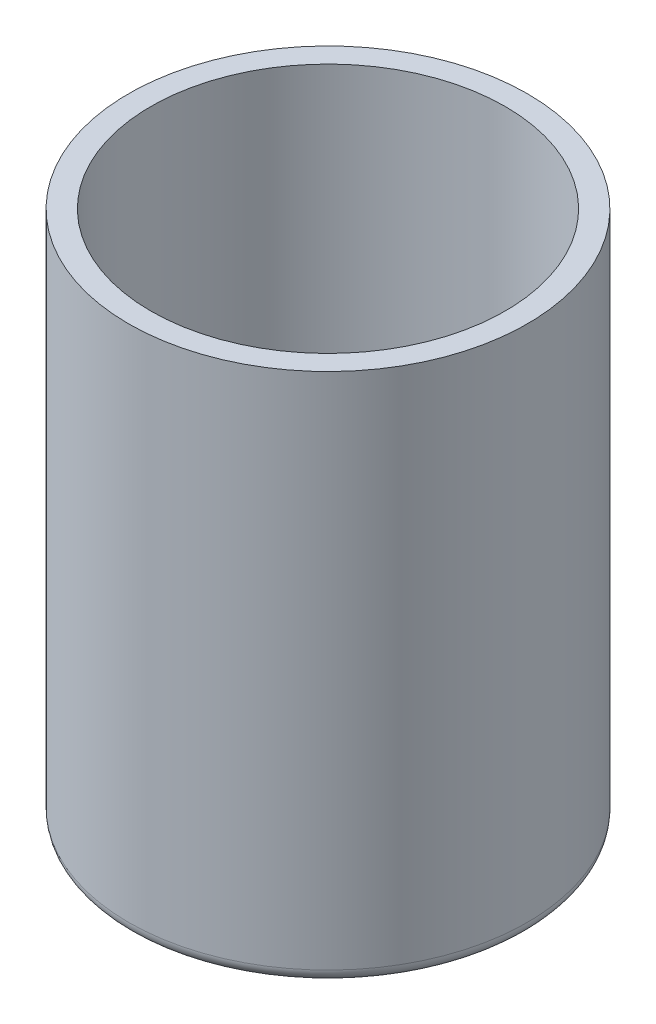
SolidWorks part; units mm, degrees
ref_plane "Front Plane" through (0, 0, 0) normal (0, 0, 1) x (1, 0, 0)
ref_plane "Top Plane" through (0, 0, 0) normal (0, 1, 0) x (1, 0, 0)
ref_plane "Right Plane" through (0, 0, 0) normal (1, 0, 0) x (0, 0, -1)
sketch "Sketch1" plane through (0, 0, 0) normal (0, 1, 0) x (1, 0, 0)
  circle A0 centre (0, 0) radius 45
extrude "Boss-Extrude1" add sketch "Sketch1" along normal blind 120
sketch "Sketch2" plane through (0, 0, 0) normal (0, 1, 0) x (1, 0, 0)
  circle A1 centre (30, 0) radius 6.2
  circle A2 centre (-30, 0) radius 6.2
sketch "Sketch3" plane through (0, 120, 0) normal (0, 1, 0) x (1, 0, 0)
  circle A0 centre (0, 0) radius 40
extrude "Cut-Extrude1" cut sketch "Sketch3" against normal blind 115
extrude "Cut-Extrude2" cut sketch "Sketch2" along normal up to surface (5 mm away) up to face at (0, 5, 40)
sketch "Sketch4" plane through (0, 0, 0) normal (0, -1, 0) x (1, 0, 0)
  circle A1 centre (0, 15) radius 3
  circle A2 centre (0, -15) radius 3
extrude "Cut-Extrude3" cut sketch "Sketch4" against normal up to surface (5 mm away) up to face at (30, 5, 6.2)
fillet "Fillet1" radius 3 1 edges at (0, 0, 45)
fillet "Fillet2" radius 1 1 edges at (-30, 0, 6.2)
fillet "Fillet3" radius 1 1 edges at (30, 0, 6.2)
fillet "Fillet4" radius 1 1 edges at (0, 0, -18)
fillet "Fillet5" radius 1 1 edges at (0, 0, 12)
sketch "Sketch5" plane through (0, 0, 0) normal (0, -1, 0) x (1, 0, 0)
  circle A0 centre (0, 0) radius 5
extrude "Cut-Extrude4" cut sketch "Sketch5" against normal up to surface (5 mm away) up to face at (0, 5, 18)
fillet "Fillet6" radius 1 1 edges at (0, 0, -5)
